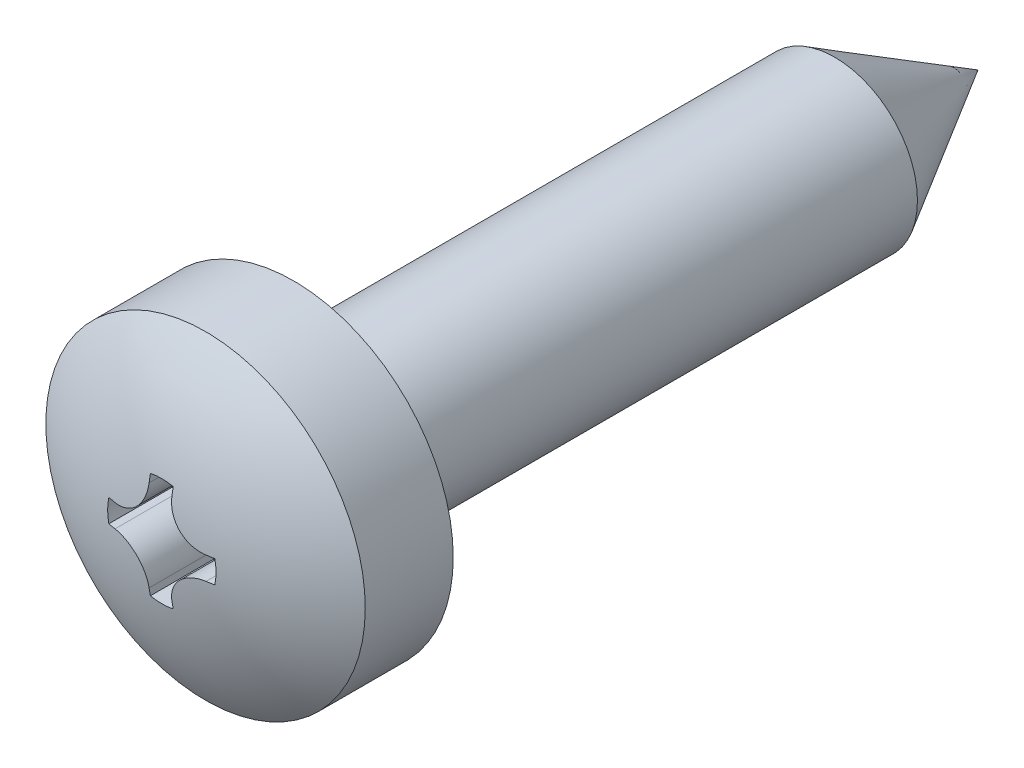
SolidWorks part; units mm, degrees
revolve "基体-旋转" add sketch "草图8" angle 360 about L0
sketch "草图8" plane through (0, 0, 0) normal (1, 0, 0) x (0, 0, -1)
  line L0 (-11.71, 0) -> (1.33, 0) construction
  line L1 (0, 0) -> (-14.4, 0)
  line L4 (-13.5425, 2.8) -> (-12, 2.8)
  line L5 (-12, 2.8) -> (-12, 1.45)
  line L6 (-12, 1.45) -> (-2.5115, 1.45)
  line L7 (-2.5115, 1.45) -> (0, 0)
  arc A0 (-14.4, 0) -> (-13.5425, 2.8) centre (-9.4, 0) cw
  dimension "D4" = 5
  dimension "D1" = 12
  dimension "D2" = 30
  dimension "D5" = 2.9
  dimension "D3" = 5.6
  dimension "D6" = 2.4
cosmetic thread "装饰螺纹线1"
extrude "切除-拉伸2" cut sketch "草图7" against normal blind 1.2
sketch "草图7" plane through (0, 0, 14.4) normal (0, 0, 1) x (1, 0, 0)
  line L0 (-7.1, 0) -> (5.9, 0) construction
  line L1 (0, 7.5) -> (0, -7) construction
  line L2 (0.2, 0.9287) -> (0.2, 0.7975)
  line L3 (0, 0) -> (4.9858, 4.9858) construction
  line L4 (0.9287, 0.2) -> (0.7975, 0.2)
  line L5 (0.9287, -0.2) -> (0.7975, -0.2)
  line L6 (0.2, -0.9287) -> (0.2, -0.7975)
  line L7 (-0.2, -0.9287) -> (-0.2, -0.7975)
  line L8 (-0.9287, -0.2) -> (-0.7975, -0.2)
  line L9 (-0.9287, 0.2) -> (-0.7975, 0.2)
  line L10 (-0.2, 0.9287) -> (-0.2, 0.7975)
  line L11 (0, 0) -> (-4.9858, 4.9858) construction
  arc A0 (-0.2, 0.9287) -> (0.2, 0.9287) centre (0, 0) cw
  arc A1 (0.9287, -0.2) -> (0.9287, 0.2) centre (0, 0) ccw
  arc A2 (0.7975, 0.2) -> (0.2, 0.7975) centre (0.7975, 0.7975) cw
  arc A3 (-0.7975, 0.2) -> (-0.2, 0.7975) centre (-0.7975, 0.7975) ccw
  arc A4 (-0.2, -0.9287) -> (0.2, -0.9287) centre (0, 0) ccw
  arc A5 (0.7975, -0.2) -> (0.2, -0.7975) centre (0.7975, -0.7975) ccw
  arc A6 (-0.9287, -0.2) -> (-0.9287, 0.2) centre (0, 0) cw
  arc A7 (-0.7975, -0.2) -> (-0.2, -0.7975) centre (-0.7975, -0.7975) cw
  dimension "D10" = 0.95
  dimension "D1" = 0.5975
  dimension "D2" = 0.5975
material "冷镦钢"
ref_plane "前视" through (0, 0, 0) normal (0, 0, 1) x (1, 0, 0)
ref_plane "上视" through (0, 0, 0) normal (0, 1, 0) x (1, 0, 0)
ref_plane "右视" through (0, 0, 0) normal (1, 0, 0) x (0, 0, -1)
sketch "尺寸草图" plane through (0, 0, 0) normal (1, 0, 0) x (0, 0, -1)
  line L0 (-12, 5.6) -> (-12, 0)
  line L1 (-12, 0) -> (0, 0)
  line L2 (0, 0) -> (0, 2.9)
  point P4 (-9.6, 0)
  point P6 (0, 1.1)
  point P7 (-10.9, 0)
  point P8 (-12, 5.5)
  point P9 (-12, 0.6)
  point P10 (-1.9, 0)
  point P11 (-1.2, 0)
  point P12 (-11.52, 0)
  point P13 (-8.5, 0)
  point P14 (-9.4, 0)
  dimension "l" = 12
  dimension "E" = 5.6
  dimension "K" = 2.4
  dimension "d" = 2.9
  dimension "P" = 1.1
  dimension "A" = 1.1
  dimension "R" = 0.1
  dimension "Rf" = 5
  dimension "HM" = 1.9
  dimension "HH" = 1.2
  dimension "HE" = 0.48
  dimension "Da" = 3.5
  dimension "Yc" = 2.6
ref_plane "基准面6" through (0, 0, 14.4) normal (0, 0, 1) x (1, 0, 0)
sketch "草图9" plane through (0, 0, 0) normal (1, 0, 0) x (0, 0, -1)
  line L0 (-10.9, 1.45) -> (-9.8, 1.45)
  line L1 (-10.9, 1.45) -> (-10.4875, 0.9)
  line L2 (-10.2125, 0.9) -> (-10.4875, 0.9)
  line L3 (-10.2125, 0.9) -> (-9.8, 1.45)
  line L4 (-11.71, 0) -> (1.33, 0) construction
  line L5 (-12, -2.8) -> (-12, 2.8) construction
  line L6 (-6.912, 0) -> (-2.6011, 0) construction
  line L7 (-13.2, 0) -> (-14.3089, 0) construction
  dimension "D1" = 1.1
  dimension "D2" = 0.275
  dimension "D3" = 0.55
  dimension "D4" = 1.45
  dimension "D5" = 1.1
revolve "切除-旋转1" [suppressed] cut sketch "草图9" angle 360 about L6
pattern_linear "阵列(线性)1" [suppressed] count 8 spacing 1.375
fillet "圆角1" radius 0.1 1 edges at (1.45, 0, 12)
equation "\"D16@基准面6\" = \"l@尺寸草图\"+\"K@尺寸草图\""
equation "\"D1@草图8\" = \"l@尺寸草图\""
equation "\"D6@草图8\" = \"K@尺寸草图\""
equation "\"D5@草图8\" = \"d@尺寸草图\""
equation "\"D3@草图8\" = \"E@尺寸草图\""
equation "\"D4@草图8\" = \"Rf@尺寸草图\""
equation "\"D10@草图7\" = \"HM@尺寸草图\"/2"
equation "\"D1@切除-拉伸2\" = \"HH@尺寸草图\""
equation "\"D1@草图9\" = \"P@尺寸草图\""
equation "\"D2@草图9\" = \"D1@草图9\"/4"
equation "\"D3@草图9\" = \"D1@草图9\"/2"
equation "\"D4@草图9\" = \"d@尺寸草图\"/2"
equation "\"D5@草图9\" = \"A@尺寸草图\""
equation "\"D3@阵列(线性)1\" = \"A@尺寸草图\"*5/4"
equation "\"D1@阵列(线性)1\" = (\"l@尺寸草图\"-\"A@尺寸草图\")/\"D3@阵列(线性)1\""
equation "\"D2@装饰螺纹线1\" = \"d@尺寸草图\"*0.866"
equation "\"D1@装饰螺纹线1\" = \"l@尺寸草图\"-\"Yc@尺寸草图\"-\"A@尺寸草图\""
equation "\"D1@圆角1\" = \"R@尺寸草图\""
